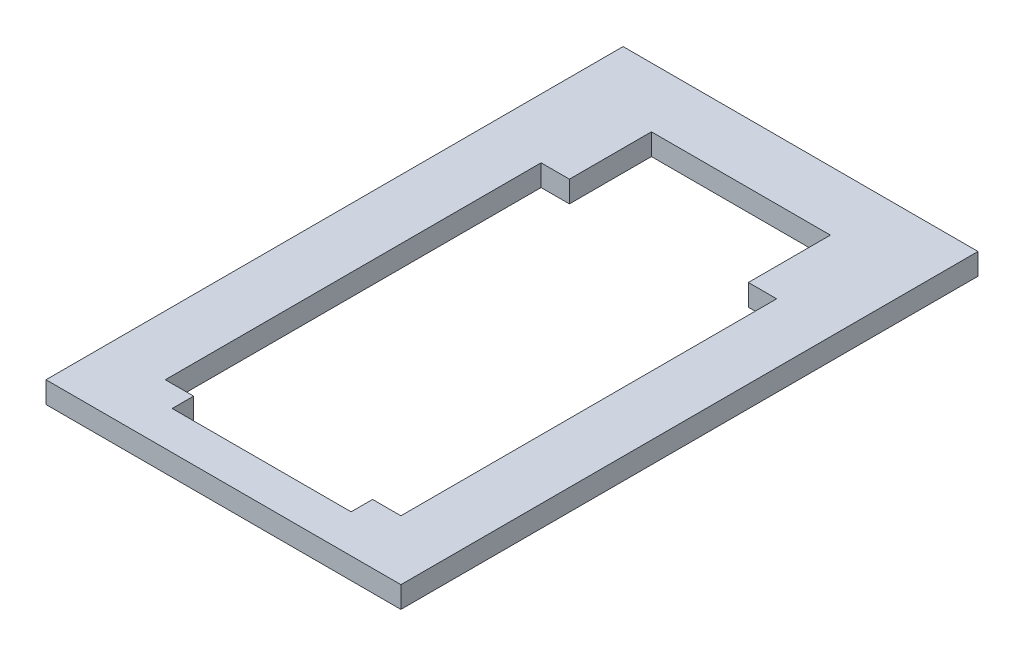
SolidWorks part; units mm, degrees
ref_plane "Front Plane" through (0, 0, 0) normal (0, 0, 1) x (1, 0, 0)
ref_plane "Top Plane" through (0, 0, 0) normal (0, 1, 0) x (1, 0, 0)
ref_plane "Right Plane" through (0, 0, 0) normal (1, 0, 0) x (0, 0, -1)
sketch "Sketch1" plane through (0, 0, 0) normal (0, 1, 0) x (1, 0, 0)
  line L1 (25.0825, -40.005) -> (-25.0825, -40.005)
  line L2 (25.0825, -40.005) -> (25.0825, 40.005)
  line L3 (25.0825, 40.005) -> (-25.0825, 40.005)
  line L4 (-25.0825, -40.005) -> (-25.0825, 40.005)
  line L5 (25.0825, -40.005) -> (-25.0825, 40.005) construction
  line L6 (25.0825, 40.005) -> (-25.0825, -40.005) construction
  line L7 (-37.7825, 52.705) -> (37.7825, 52.705)
  line L8 (-37.7825, 52.705) -> (-37.7825, -52.705)
  line L9 (-37.7825, -52.705) -> (37.7825, -52.705)
  line L10 (37.7825, 52.705) -> (37.7825, -52.705)
  line L11 (-37.7825, 52.705) -> (37.7825, -52.705) construction
  line L12 (-37.7825, -52.705) -> (37.7825, 52.705) construction
  point P0 (0, 0)
  point P6 (0, 0)
  dimension "D1" = 80.01
  dimension "D2" = 50.165
  dimension "D3" = 12.7
  dimension "D4" = 12.7
extrude "Boss-Extrude1" add sketch "Sketch1" along normal blind 4.572
sketch "Sketch2" plane through (0, 4.572, 0) normal (0, 1, 0) x (1, 0, 0)
  line L0 (-25.0825, -40.005) -> (25.0825, -40.005) construction
  line L1 (-19.05, -40.005) -> (19.05, -40.005)
  line L2 (-19.05, -40.005) -> (-19.05, -44.577)
  line L3 (-19.05, -44.577) -> (19.05, -44.577)
  line L4 (19.05, -40.005) -> (19.05, -44.577)
  line L5 (25.0825, 40.005) -> (-25.0825, 40.005) construction
  line L6 (-19.05, 40.005) -> (19.05, 40.005)
  line L7 (-19.05, 40.005) -> (-19.05, 48.133)
  line L8 (-19.05, 48.133) -> (19.05, 48.133)
  line L9 (19.05, 40.005) -> (19.05, 48.133)
  point P6 (0, -40.005)
  point P14 (0, 40.005)
  dimension "D1" = 4.572
  dimension "D2" = 38.1
  dimension "D3" = 8.128
  dimension "D4" = 38.1
extrude "Cut-Extrude1" cut sketch "Sketch2" against normal through all
sketch "Sketch3" plane through (0, 4.572, 0) normal (0, 1, 0) x (1, 0, 0)
  line L0 (-19.05, 48.133) -> (19.05, 48.133)
  line L1 (-19.05, 48.133) -> (-19.05, 52.705)
  line L2 (19.05, 48.133) -> (19.05, 52.705)
  line L3 (-19.05, 52.705) -> (19.05, 52.705)
  line L4 (37.7825, 52.705) -> (-37.7825, 52.705) construction
  point P0 (19.05, 52.705)
extrude "Cut-Extrude2" cut sketch "Sketch3" against normal through all
sketch "Sketch4" plane through (0, 4.572, 0) normal (0, 1, 0) x (1, 0, 0)
  line L0 (-19.05, 52.705) -> (-37.7825, 52.705)
  line L1 (-19.05, 52.705) -> (-19.05, 57.4675)
  line L2 (-37.7825, 52.705) -> (-37.7825, 57.4675)
  line L3 (-19.05, 57.4675) -> (-37.7825, 57.4675)
  line L4 (37.7825, 52.705) -> (19.05, 52.705)
  line L5 (37.7825, 52.705) -> (37.7825, 57.4675)
  line L6 (19.05, 52.705) -> (19.05, 57.4675)
  line L7 (37.7825, 57.4675) -> (19.05, 57.4675)
  line L8 (37.7825, 57.4675) -> (-37.7825, 57.4675)
  line L9 (37.7825, 57.4675) -> (37.7825, 70.1675)
  line L10 (-37.7825, 57.4675) -> (-37.7825, 70.1675)
  line L11 (37.7825, 70.1675) -> (-37.7825, 70.1675)
  point P9 (0, 0)
  point P16 (0, 0)
  line M7 (-19.05, 52.705) -> (-37.7825, 52.705)
  line M11 (37.7825, 52.705) -> (19.05, 52.705)
  dimension "D1" = 4.7625
  dimension "D2" = 12.7
extrude "Boss-Extrude2" add sketch "Sketch4" against normal up to surface (4.572 mm away) contours L9 L11 L10 L3 L8 L7 | L1 L3 L2 M7 | L5 L7 L6 M11 up to face at (0, 0, -1.016)
